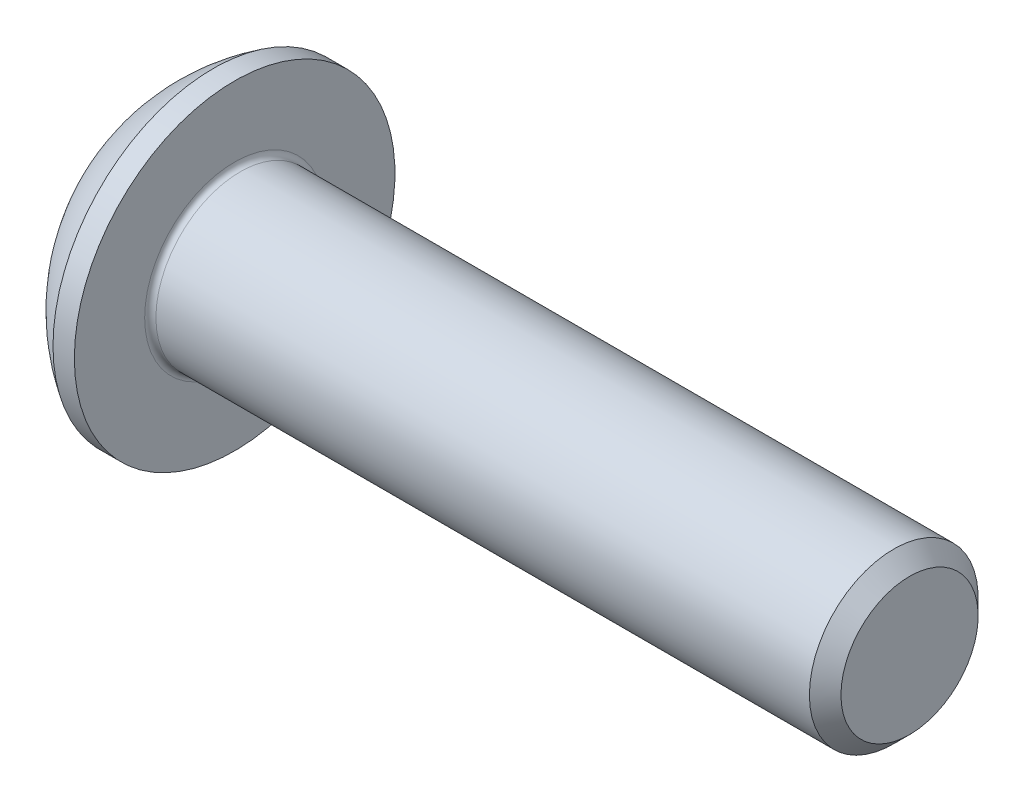
SolidWorks part; units mm, degrees
ref_plane "Plane1" through (0, 0, 0) normal (0, 0, 1) x (1, 0, 0)
ref_plane "Plane2" through (0, 0, 0) normal (0, 1, 0) x (1, 0, 0)
ref_plane "Plane3" through (0, 0, 0) normal (1, 0, 0) x (0, 0, -1)
sketch "BodySke" plane through (0, 0, 0) normal (0, 0, 1) x (1, 0, 0)
  line L0 (13.65, 0) -> (13.65, 1.2195)
  line L1 (13.3695, 1.5) -> (1.65, 1.5)
  line L2 (1.65, 1.5) -> (1.65, 2.85)
  line L3 (1.65, 2.85) -> (1.27, 2.85)
  line L4 (0, 0) -> (101.6, 0) construction
  line L5 (1.65, -2.85) -> (1.27, -2.85) construction
  line L6 (55.6768, -1.5) -> (1.65, -1.5) construction
  line L7 (13.65, 0) -> (0, 0)
  line L8 (0, 1.425) -> (0, -1.425) construction
  line L9 (0, 0) -> (0, 1.425)
  line L10 (13.65, 1.2195) -> (13.3695, 1.5)
  line L11 (13.65, -1.2195) -> (13.3695, -1.5) construction
  line L12 (2.15, 9.525) -> (2.15, -1.5) construction
  line L13 (7.65, 9.525) -> (7.65, -1.5) construction
  arc A1 (0, 1.425) -> (1.27, 2.85) centre (3.0334, 0) cw
  dimension "Diameter" = 3
  dimension "Length" = 12
  dimension "Head_dia" = 5.7
  dimension "D1" = 2.85
  dimension "Head_ht" = 1.65
  dimension "Head_side_ht" = 0.38
  dimension "Minor_dia" = 2.439
  dimension "Body_ch_ang" = 45
  dimension "Advance" = 0.5
revolve "BaseBody" add sketch "BodySke" angle 360 about L4
cosmetic thread "ThreadCosmetic" [suppressed] parameters "Thread_length"=6, "Thread_minor"=2.439
fillet "Fillet1" radius 0.1 1 edges at (1.65, 0, 1.5)
sketch "Sketch2" plane through (0, 0, 0) normal (0, 0, 1) x (1, 0, 0)
  line L0 (0, 1) -> (1.04, 1)
  line L1 (1.04, 1) -> (1.6174, 0)
  line L3 (1.6174, 0) -> (0, 0)
  line L4 (0, 0) -> (0, 1)
  line L5 (0, -1) -> (1.04, -1) construction
  line L6 (0, 0) -> (47.625, 0) construction
  dimension "D2" = 60
  dimension "PreBroach_depth" = 1.04
  dimension "PreBroach_dia" = 2
revolve "PreBroach" cut sketch "Sketch2" angle 360 about L6
sketch "Sketch3" plane through (0, 0, 0) normal (1, 0, 0) x (0, 0, -1)
  line L0 (-1, -0.5774) -> (-1, 0.5774)
  line L1 (-1, 0.5774) -> (0, 1.1547)
  line L2 (0, 1.1547) -> (1, 0.5774)
  line L3 (1, 0.5774) -> (1, -0.5774)
  line L4 (1, -0.5774) -> (0, -1.1547)
  line L5 (0, -1.1547) -> (-1, -0.5774)
  dimension "Hex_size" = 2
  dimension "D3" = 2
  dimension "D1" = 1
  dimension "D2" = 1
extrude "Hex" cut sketch "Sketch3" along normal blind 1.04
sketch "ThdSchSke" plane through (0, 0, 0) normal (0, 0, 1) x (1, 0, 0)
  line L0 (7.65, -1.2195) -> (7.4536, -1.5)
  line L1 (7.65, -1.2195) -> (7.8464, -1.5)
  line L2 (7.8464, -1.5) -> (7.8464, -1.875)
  line L3 (-3.175, 0) -> (5.1513, 0) construction
  line L5 (7.8464, -1.875) -> (7.4536, -1.875)
  line L6 (7.4536, -1.875) -> (7.4536, -1.5)
  dimension "Diameter" = 3
  dimension "Thread_minor" = 2.439
  dimension "SideAngle" = 55
  dimension "VeeAngle" = 70
  dimension "Overcut" = 3.75
revolve "ThreadSchematic" [suppressed] cut sketch "ThdSchSke" angle 360 about L3
pattern_linear "ThdSchPat" [suppressed]
equation "\"D1@BodySke\" = \"Head_dia@BodySke\" * .5"
equation "\"Thread_minor@ThreadCosmetic\" = \"Minor_dia@BodySke\""
equation "\"D1@Sketch3\" = \"Hex_size@Sketch3\" / 2"
equation "\"D2@Sketch3\" = \"D1@Sketch3\""
equation "\"D3@Sketch3\" = \"Hex_size@Sketch3\""
equation "\"Thread_length@ThreadCosmetic\" = ((sgn( (\"Length@BodySke\" - \"Advance@BodySke\" * 2.0) - \"Thread_nom@BodySke\" )-1)*( (\"Length@BodySke\" - \"Advance@BodySke\" * 2.0) - \"Thread_nom@BodySke\" ))/-2+ \"Thread_nom@BodySke\""
equation "\"Thread_minor@ThdSchSke\" = \"Minor_dia@BodySke\""
equation "\"Diameter@ThdSchSke\" = \"Diameter@BodySke\""
equation "\"Overcut@ThdSchSke\" = \"Diameter@BodySke\" * 1.25"
equation "\"Start@ThdSchSke\" = \"Head_ht@BodySke\" + \"Length@BodySke\" - \"Thread_length@ThreadCosmetic\"  '---Non-countersunk---"
equation "\"Num_threads@ThdSchPat\" = int( \"Thread_length@ThreadCosmetic\" / \"Advance@BodySke\" + 0.999 )  + 1"
equation "\"Advance@ThdSchPat\" = \"Thread_length@ThreadCosmetic\" /  (\"Num_threads@ThdSchPat\" - 1) 'relax it"
equation "\"Num_threads@ThdSchPat\" = \"Num_threads@ThdSchPat\" - sgn( \"Num_threads@ThdSchPat\" - 1) '---chamfered tips only---"
